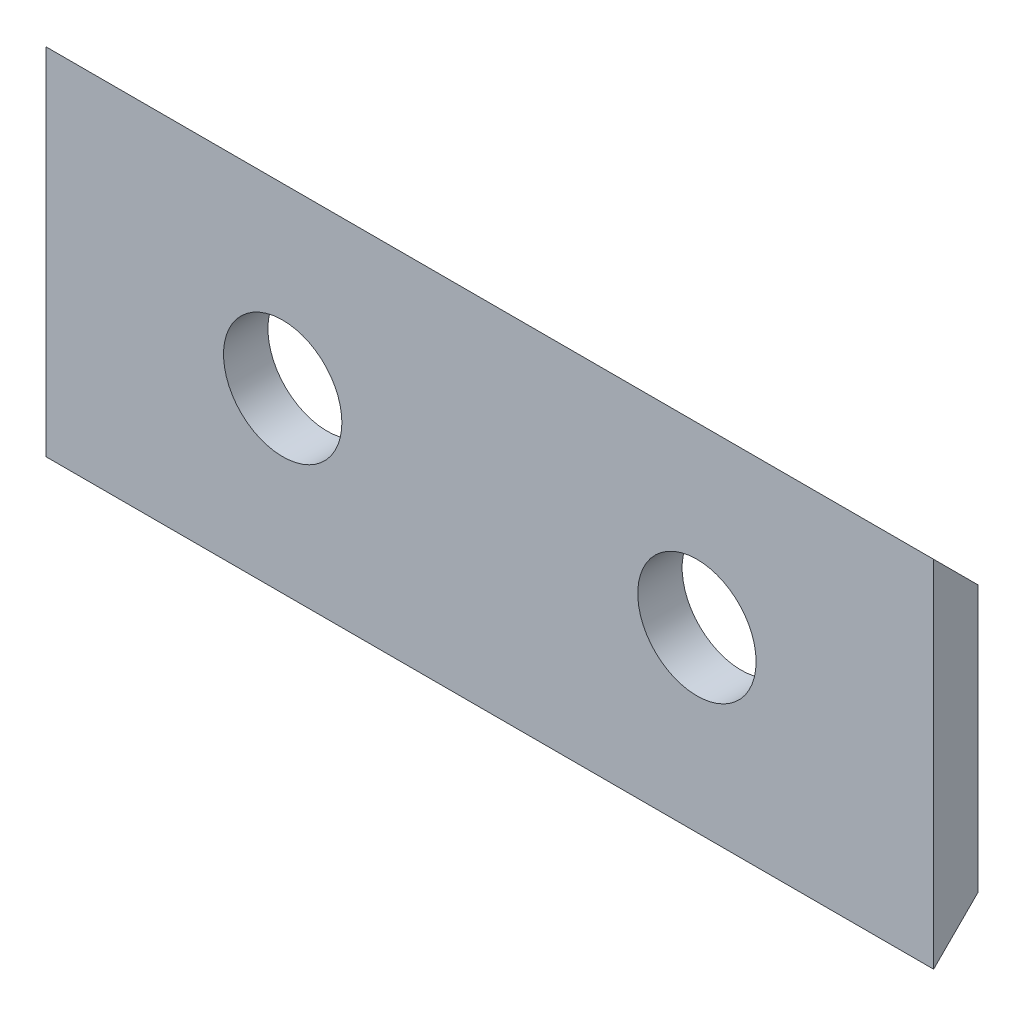
SolidWorks part; units mm, degrees
ref_plane "Front Plane" through (0, 0, 0) normal (0, 0, 1) x (1, 0, 0)
ref_plane "Top Plane" through (0, 0, 0) normal (0, 1, 0) x (1, 0, 0)
ref_plane "Right Plane" through (0, 0, 0) normal (1, 0, 0) x (0, 0, -1)
sketch "Sketch1" plane through (0, 0, 0) normal (0, 0, 1) x (1, 0, 0)
  line L1 (0, 0) -> (-30, 0)
  line L2 (0, 0) -> (0, 12)
  line L3 (0, 12) -> (-30, 12)
  line L4 (-30, 0) -> (-30, 12)
  circle A0 centre (-22, 6) radius 2
  circle A1 centre (-8, 6) radius 2
  dimension "D3" = 4
  dimension "D4" = 4
  dimension "D6" = 14
  dimension "D7" = 8
  dimension "D1" = 30
  dimension "D2" = 12
  dimension "D5" = 6
extrude "Boss-Extrude1" add sketch "Sketch1" along normal blind 1.5
sketch "Sketch2" plane through (0, 0, 0) normal (1, 0, 0) x (0, 0, -1)
  line L0 (0, 12) -> (-1.5, 12)
  line L1 (-1.5, 12) -> (0, 10.5)
  line L2 (0, 0) -> (0, 12) construction
  line L3 (0, 10.5) -> (0, 12)
  line L4 (0, 0) -> (0, 1.5)
  line L5 (0, 1.5) -> (-1.5, 0)
  line L6 (-1.5, 0) -> (0, 0)
  dimension "D1" = 45
  dimension "D2" = 45
extrude "Cut-Extrude1" cut sketch "Sketch2" against normal through all
